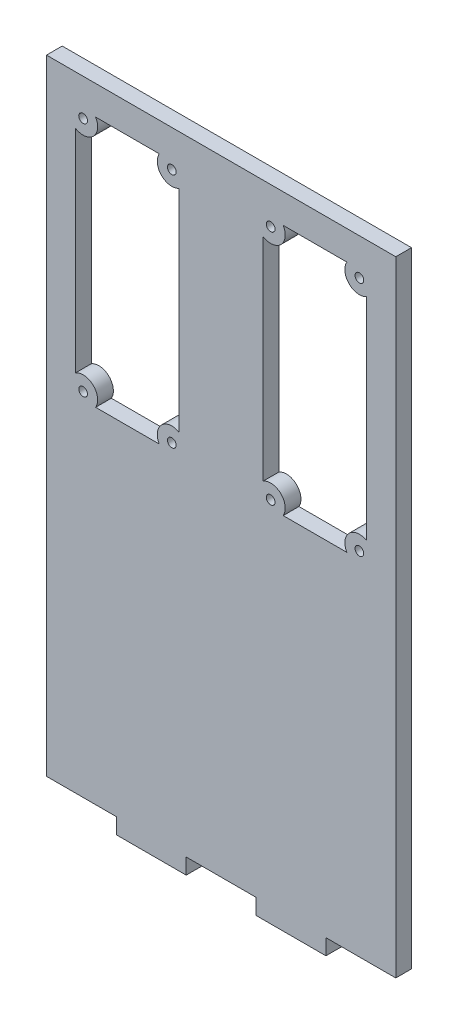
SolidWorks part; units mm, degrees
ref_plane "Ön Düzlem" through (0, 0, 0) normal (0, 0, 1) x (1, 0, 0)
ref_plane "Üst Düzlem" through (0, 0, 0) normal (0, 1, 0) x (1, 0, 0)
ref_plane "Sağ Düzlem" through (0, 0, 0) normal (1, 0, 0) x (0, 0, -1)
sketch "Sketch1" plane through (0, 0, 0) normal (0, 0, 1) x (1, 0, 0)
  line L14 (-30.0721, -52.4126) -> (-30.0721, 54.8874)
  line L21 (29.9279, 54.8874) -> (-30.0721, 54.8874)
  line L25 (17.9279, -55.1126) -> (5.9279, -55.1126)
  line L26 (-6.0721, -55.1126) -> (-18.0721, -55.1126)
  line L27 (-18.0721, -55.1126) -> (-18.0721, -52.4126)
  line L28 (-18.0721, -52.4126) -> (-30.0721, -52.4126)
  line L29 (-6.0721, -55.1126) -> (-6.0721, -52.4126)
  line L30 (-6.0721, -52.4126) -> (5.9279, -52.4126)
  line L31 (5.9279, -55.1126) -> (5.9279, -52.4126)
  line L32 (17.9279, -55.1126) -> (17.9279, -52.4126)
  line L33 (17.9279, -52.4126) -> (29.9279, -52.4126)
  line L34 (29.9279, 54.8874) -> (29.9279, -52.4126)
  line L37 (-10.6972, 49.8874) -> (-21.6304, 49.8874)
  line L38 (-10.6972, 6.7074) -> (-21.6304, 6.7074)
  line L40 (-7.2921, 46.4533) -> (-7.2921, 10.1415)
  line L41 (-25.0721, 46.4749) -> (-25.0721, 10.1199)
  line L43 (21.5228, 49.8874) -> (10.5896, 49.8874)
  line L44 (21.5228, 6.7074) -> (10.5896, 6.7074)
  line L46 (24.9279, 46.4533) -> (24.9279, 10.1415)
  line L47 (7.1479, 46.4749) -> (7.1479, 10.1199)
  arc A13 (10.5896, 6.7074) -> (7.1479, 10.1199) centre (8.4362, 7.9774) ccw
  arc A14 (24.9279, 10.1415) -> (21.5228, 6.7074) centre (23.6762, 7.9774) ccw
  arc A15 (7.1479, 46.4749) -> (10.5896, 49.8874) centre (8.4362, 48.6174) ccw
  circle A23 centre (-8.5438, 48.6174) radius 0.75
  circle A27 centre (-8.5438, 7.9774) radius 0.75
  circle A29 centre (-23.7838, 7.9774) radius 0.75
  circle A30 centre (-23.7838, 48.6174) radius 0.75
  circle A31 centre (23.6762, 48.6174) radius 0.75
  circle A35 centre (23.6762, 7.9774) radius 0.75
  circle A37 centre (8.4362, 7.9774) radius 0.75
  circle A38 centre (8.4362, 48.6174) radius 0.75
  arc A39 (21.5228, 49.8874) -> (24.9279, 46.4533) centre (23.6762, 48.6174) ccw
  arc A40 (-10.6972, 49.8874) -> (-7.2921, 46.4533) centre (-8.5438, 48.6174) ccw
  arc A41 (-25.0721, 46.4749) -> (-21.6304, 49.8874) centre (-23.7838, 48.6174) ccw
  arc A42 (-21.6304, 6.7074) -> (-25.0721, 10.1199) centre (-23.7838, 7.9774) ccw
  arc A43 (-7.2921, 10.1415) -> (-10.6972, 6.7074) centre (-8.5438, 7.9774) ccw
  point P0 (-0.0721, -5.1126)
  point P17 (-16.1821, 28.2974)
  point P64 (16.0379, 28.2974)
extrude "Boss-Extrude1" add sketch "Sketch1" along normal blind 2.7
